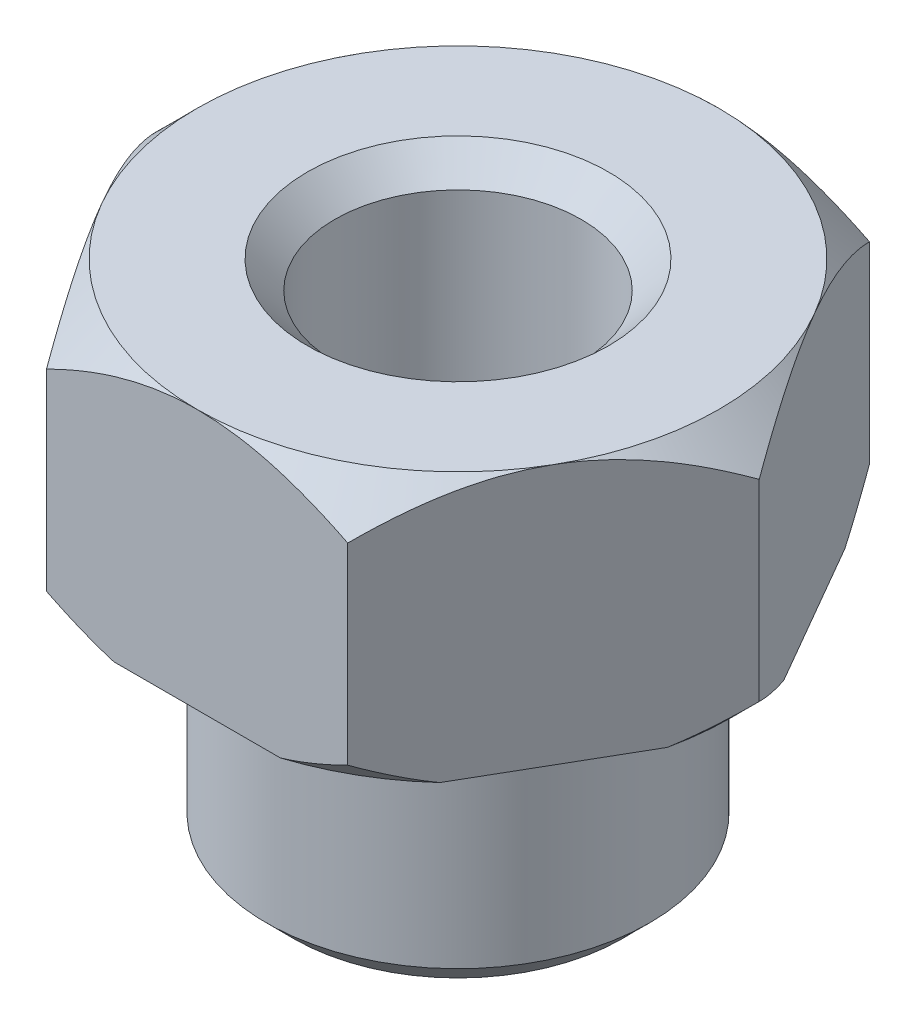
SolidWorks part; units mm, degrees
ref_plane "Alzado" through (0, 0, 0) normal (0, 0, 1) x (1, 0, 0)
ref_plane "Planta" through (0, 0, 0) normal (0, 1, 0) x (1, 0, 0)
ref_plane "Vista lateral" through (0, 0, 0) normal (1, 0, 0) x (0, 0, -1)
sketch "Croquis1" plane through (0, 0, 0) normal (0, 0, 1) x (1, 0, 0)
  line L0 (0, 51.9305) -> (0, -46.2059) construction
  line L1 (6.35, 31.3792) -> (20, 31.3792)
  line L2 (22, 29.3792) -> (22, 14.3792)
  line L3 (20, 12.3792) -> (14, 12.3792)
  line L4 (14, 9.0205) -> (14, -3.6208)
  line L5 (12, -5.6208) -> (1.5875, -5.6208)
  line L6 (6.35, 31.3792) -> (6.35, 12.3792)
  line L7 (14, 12.3792) -> (13.0766, 12.3792)
  line L8 (13.0766, 12.3792) -> (13.0766, 9.7063)
  line L9 (13.0766, 9.7063) -> (14, 9.0205)
  line L10 (14, -3.6208) -> (12, -5.6208)
  line L11 (22, 14.3792) -> (20, 12.3792)
  line L12 (20, 31.3792) -> (22, 29.3792)
  line L13 (6.35, 12.3792) -> (1.5875, 12.3792)
  line L14 (1.5875, 12.3792) -> (1.5875, -5.6208)
  point P4 (22, 31.3792)
  point P6 (22, 12.3792)
  point P8 (14, -5.6208)
  dimension "D1" = 14
  dimension "D2" = 22
  dimension "D6" = 18
  dimension "D7" = 15
  dimension "D8" = 1.5875
  dimension "D9" = 22
  dimension "D10" = 6.35
  dimension "D11" = 19
revolve "Revolución1" add sketch "Croquis1" angle 360 about L0
sketch "Croquis4" plane through (0, 31.3792, 0) normal (0, 1, 0) x (1, 0, 0)
  line L1 (22, 0) -> (11, 19.0526)
  line L2 (11, 19.0526) -> (-11, 19.0526)
  line L3 (-11, 19.0526) -> (-22, 0)
  line L4 (-22, 0) -> (-11, -19.0526)
  line L5 (-11, -19.0526) -> (11, -19.0526)
  line L6 (11, -19.0526) -> (22, 0)
  circle A0 centre (0, 0) radius 19.0526 construction
extrude "Cortar-Extruir6" cut sketch "Croquis4" against normal blind 70 flip side to cut
sketch "Croquis5" plane through (0, 31.3792, 0) normal (0, 1, 0) x (1, 0, 0)
  circle A0 centre (0, 0) radius 19.0526
extrude "Cortar-Extruir7" cut sketch "Croquis5" against normal blind 70 draft 45 flip side to cut
sketch "Croquis6" plane through (0, 31.3792, 0) normal (0, 1, 0) x (1, 0, 0)
  circle A0 centre (0, 0) radius 9
  dimension "D1" = 18
extrude "Cortar-Extruir8" cut sketch "Croquis6" against normal blind 15
chamfer "Chaflán1" distance 2 angle 45 1 edges at (-9, 31.3792, 0)
fillet "Redondeo1" radius 1 1 edges at (-6.35, 16.3792, 0)
